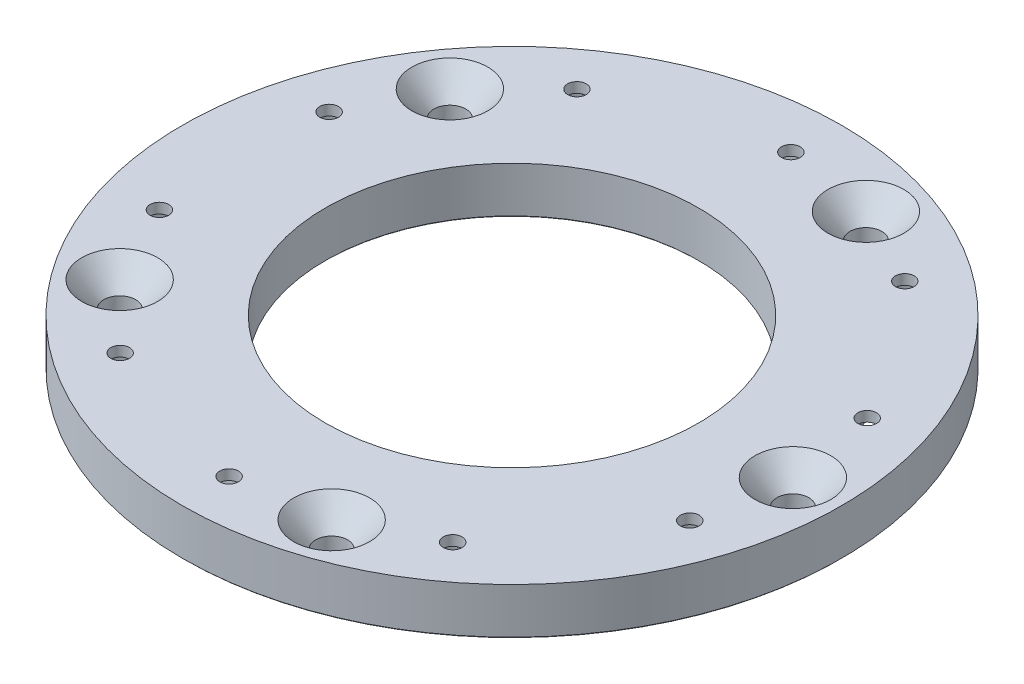
SolidWorks part; units mm, degrees
material "6061-T6 (SS)"
ref_plane "Front Plane" through (0, 0, 0) normal (0, 0, 1) x (1, 0, 0)
ref_plane "Top Plane" through (0, 0, 0) normal (0, 1, 0) x (1, 0, 0)
ref_plane "Right Plane" through (0, 0, 0) normal (1, 0, 0) x (0, 0, -1)
sketch "Sketch1" plane through (0, 0, 0) normal (0, 0, 1) x (1, 0, 0)
  line L0 (31.623, 0) -> (31.623, -7.9375)
  line L1 (31.623, -7.9375) -> (34.163, -7.9375)
  line L2 (34.163, -7.9375) -> (34.163, -3.9497)
  line L3 (34.163, -3.9497) -> (41.275, -3.9497)
  line L4 (41.275, -3.9497) -> (41.275, -7.9375)
  line L5 (41.275, -7.9375) -> (55.88, -7.9375)
  line L6 (55.88, -7.9375) -> (55.88, 0)
  line L9 (55.88, 0) -> (31.623, 0)
  line L10 (0, 29.8764) -> (0, -28.8743) construction
  dimension "D1" = 2.54
  dimension "D2" = 7.112
  dimension "D3" = 111.76
  dimension "D4" = 3.9878
  dimension "D5" = 7.9375
  dimension "D6" = 82.55
revolve "Revolve1" add sketch "Sketch1" angle 360 about L10
sketch "Sketch2" plane through (0, 0, 0) normal (0, 1, 0) x (-1, 0, 0)
  line L0 (0, 0) -> (-47.625, 0) construction
  line L1 (0, 0) -> (-14.7169, 45.2941) construction
  line L2 (0, 0) -> (38.5294, 27.9933) construction
  line L3 (0, 0) -> (38.5294, -27.9933) construction
  line L4 (0, 0) -> (-14.7169, -45.2941) construction
  circle A0 centre (0, 0) radius 47.625 construction
  point P3 (38.5294, -27.9933)
  point P4 (-14.7169, -45.2941)
  point P5 (-47.625, 0)
  point P6 (-14.7169, 45.2941)
  point P7 (38.5294, 27.9933)
  dimension "D1" = 95.25
  dimension "D2" = 72
  dimension "D3" = 72
  dimension "D4" = 72
  dimension "D5" = 72
hole_wizard "CSK for 1/4 Flat Head Machine Screw1" positions "Sketch4" profile "Sketch3" countersink size "1/4" standard "Ansi Inch" end condition through all
sketch "Sketch4" plane through (0, 0, 0) normal (0, 1, 0) x (-1, 0, 0)
  circle A0 centre (0, 0) radius 47.625 construction
  point P0 (-47.625, 0)
  point P3 (-14.7169, 45.2941)
  point P5 (38.5294, 27.9933)
  point P7 (38.5294, -27.9933)
  point P11 (-14.7169, -45.2941)
sketch "Sketch3" plane through (47.625, 0, 0) normal (1, 0, 0) x (0, 0, 1)
  line L0 (0, 0) -> (0, 7.9375)
  line L1 (0, 7.9375) -> (2.7051, 7.9375)
  line L2 (2.7051, 7.9375) -> (2.7051, 4.2952)
  line L3 (2.7051, 4.2952) -> (6.4389, 0)
  line L5 (6.4389, 0) -> (0, 0)
  line L6 (-2.7051, 4.2952) -> (-6.4389, 0) construction
  line L11 (0, -6.35) -> (0, 107.95) construction
  dimension "Thru Hole Dia." = 5.4102
  dimension "Thru Hole Depth" = 7.9375
  dimension "Near C'Sink Dia." = 12.8778
  dimension "Near C'Sink Angle" = 82
sketch "Sketch5" plane through (0, 0, 0) normal (0, 1, 0) x (1, 0, 0)
  circle A0 centre (-27.7143, 38.7306) radius 1.5875
  circle A1 centre (0, 0) radius 47.625 construction
  circle A2 centre (-38.5294, -27.9933) radius 6.4389 construction
  circle A3 centre (-0.3439, 47.6238) radius 1.5875
  circle A4 centre (28.2708, 38.3263) radius 1.5875
  circle A5 centre (45.1866, 15.0437) radius 1.5875
  circle A6 centre (45.1866, -15.0437) radius 1.5875
  circle A7 centre (28.2708, -38.3263) radius 1.5875
  circle A8 centre (-0.3439, -47.6238) radius 1.5875
  circle A9 centre (-27.7143, -38.7306) radius 1.5875
  circle A10 centre (-45.3992, -14.3894) radius 1.5875
  circle A11 centre (-45.3992, 14.3894) radius 1.5875
  circle A12 centre (14.7169, -45.2941) radius 6.4389 construction
  circle A13 centre (47.625, 0) radius 6.4389 construction
  circle A15 centre (14.7169, 45.2941) radius 6.4389 construction
  circle A16 centre (-38.5294, 27.9933) radius 6.4389 construction
  dimension "D1" = 3.175
  dimension "D3" = 95.25
extrude "Rivet Holes" cut sketch "Sketch5" against normal through all
sketch "Sketch6" plane through (0, -7.9375, 0) normal (0, -1, 0) x (1, 0, 0)
  arc A0 (45.1866, 15.0437) -> (28.2708, 38.3263) centre (0, 0) ccw construction
  arc A2 (48.9522, 16.2973) -> (30.6267, 41.5201) centre (0, 0) ccw
  arc A3 (41.4211, 13.79) -> (25.9149, 35.1324) centre (0, 0) ccw
  arc A4 (41.4211, 13.79) -> (48.9522, 16.2973) centre (45.1866, 15.0437) ccw
  arc A5 (30.6267, 41.5201) -> (25.9149, 35.1324) centre (28.2708, 38.3263) ccw
  arc A13 (-0.3439, 47.6238) -> (-27.7143, 38.7306) centre (0, 0) ccw construction
  arc A14 (-0.3726, 51.5924) -> (-30.0238, 41.9581) centre (0, 0) ccw
  arc A15 (-0.3153, 43.6551) -> (-25.4048, 35.503) centre (0, 0) ccw
  arc A16 (-0.3153, 43.6551) -> (-0.3726, 51.5924) centre (-0.3439, 47.6238) ccw
  arc A17 (-30.0238, 41.9581) -> (-25.4048, 35.503) centre (-27.7143, 38.7306) ccw
  arc A18 (-45.3992, 14.3894) -> (-45.3992, -14.3894) centre (0, 0) ccw construction
  arc A19 (-49.1824, 15.5886) -> (-49.1824, -15.5886) centre (0, 0) ccw
  arc A20 (-41.6159, 13.1903) -> (-41.6159, -13.1903) centre (0, 0) ccw
  arc A21 (-41.6159, 13.1903) -> (-49.1824, 15.5886) centre (-45.3992, 14.3894) ccw
  arc A22 (-49.1824, -15.5886) -> (-41.6159, -13.1903) centre (-45.3992, -14.3894) ccw
  arc A23 (-27.7143, -38.7306) -> (-0.3439, -47.6238) centre (0, 0) ccw construction
  arc A24 (-30.0238, -41.9581) -> (-0.3726, -51.5924) centre (0, 0) ccw
  arc A25 (-25.4048, -35.503) -> (-0.3153, -43.6551) centre (0, 0) ccw
  arc A26 (-25.4048, -35.503) -> (-30.0238, -41.9581) centre (-27.7143, -38.7306) ccw
  arc A27 (-0.3726, -51.5924) -> (-0.3153, -43.6551) centre (-0.3439, -47.6238) ccw
  arc A28 (28.2708, -38.3263) -> (45.1866, -15.0437) centre (0, 0) ccw construction
  arc A29 (30.6267, -41.5201) -> (48.9522, -16.2973) centre (0, 0) ccw
  arc A30 (25.9149, -35.1324) -> (41.4211, -13.79) centre (0, 0) ccw
  arc A31 (25.9149, -35.1324) -> (30.6267, -41.5201) centre (28.2708, -38.3263) ccw
  arc A32 (48.9522, -16.2973) -> (41.4211, -13.79) centre (45.1866, -15.0437) ccw
  point P5 (38.5294, 27.9933)
  point P10 (-14.7169, 45.2941)
  point P28 (-47.625, 0)
  point P33 (-14.7169, -45.2941)
  point P42 (38.5294, -27.9933)
  dimension "D1" = 7.9375
extrude "Cut-Extrude2" cut sketch "Sketch6" against normal offset from surface (6.2103 mm away) 1.7272 up to face at (-45.3992, 0, -12.8019)
chamfer "Chamfer1" distance 0.2032 angle 45 4 edges at (0, -7.9375, 55.88) (0, -7.9375, 41.275) (0, -7.9375, 34.163) (0, -7.9375, 31.623)
